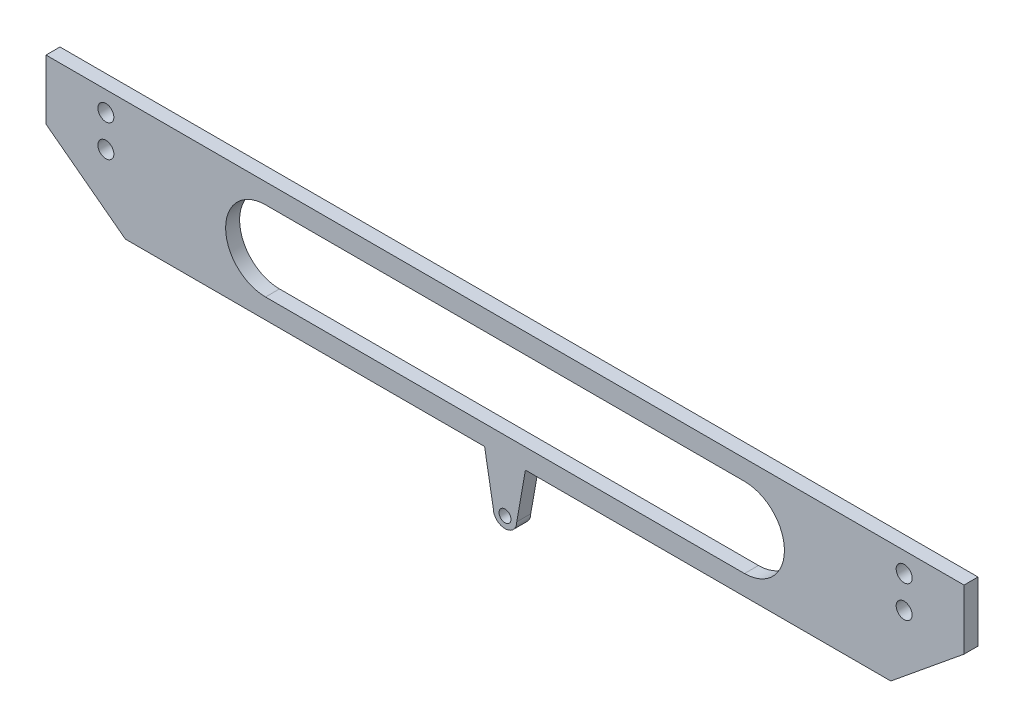
SolidWorks part; units mm, degrees
material "Acrylic (Medium-high impact)"
ref_plane "Front Plane" through (0, 0, 0) normal (0, 0, 1) x (1, 0, 0)
ref_plane "Top Plane" through (0, 0, 0) normal (0, 1, 0) x (1, 0, 0)
ref_plane "Right Plane" through (0, 0, 0) normal (1, 0, 0) x (0, 0, -1)
sketch "Sketch1" plane through (0, 0, 0) normal (0, 0, 1) x (1, 0, 0)
  line L0 (65, 0) -> (-65, 0) construction
  line L1 (-65, 0) -> (0, 65) construction
  line L2 (0, 65) -> (65, 0) construction
  line L3 (0, 65) -> (130, 65) construction
  line L4 (130, 65) -> (195, 0) construction
  circle A0 centre (-65, 0) radius 30
  circle A1 centre (65, 0) radius 30
  circle A2 centre (195, 0) radius 30
  point P4 (0, 0)
  dimension "D2" = 60
  dimension "D1" = 130
  dimension "D3" = 90
  dimension "D4" = 91.9239
  dimension "D5" = 135
  dimension "D6" = 130
sketch "Sketch2" plane through (0, 0, 0) normal (0, 0, 1) x (1, 0, 0)
  line L4 (-56.1612, -8.8388) -> (0, 47.3223)
  line L5 (0, 47.3223) -> (56.1612, -8.8388)
  line L6 (-73.8388, 8.8388) -> (0, 82.6777)
  line L7 (0, 82.6777) -> (73.8388, 8.8388)
  line L19 (56.1612, -8.8388) -> (0, 47.3223)
  circle A0 centre (-65, 0) radius 3.5
  circle A1 centre (65, 0) radius 3.5
  arc A4 (56.1612, -8.8388) -> (73.8388, 8.8388) centre (65, 0) ccw
  arc A5 (-73.8388, 8.8388) -> (-56.1612, -8.8388) centre (-65, 0) ccw
  circle A6 centre (65, 0) radius 3.5
  circle A7 centre (0, 65) radius 1.5
  point P18 (-65, 0)
  dimension "D6" = 3
  dimension "D1" = 25
  dimension "D2" = 90
sketch "Sketch3" plane through (0, 0, 0) normal (0, 0, 1) x (1, 0, 0)
  line L0 (5.5606, 53.0357) -> (0, 47.3223)
  line L1 (-56.1612, -8.8388) -> (0, 47.3223) construction
  line L2 (-73.8388, 8.8388) -> (0, 82.6777) construction
  line L3 (0, 47.3223) -> (-17.6777, 65)
  line L4 (5.5606, 53.0357) -> (124.8223, 52.5)
  line L5 (124.8223, 52.5) -> (186.1612, -8.8388)
  line L6 (-5.1777, 77.5) -> (59.8841, 77.5)
  line L7 (135.1777, 77.5) -> (203.8388, 8.8388)
  line L8 (-17.6777, 65) -> (-5.1777, 77.5)
  line L9 (0, 65) -> (130, 65) construction
  line L10 (0, 47.3223) -> (56.1612, -8.8388) construction
  line L11 (65, 77.5) -> (65, 89.5) construction
  line L12 (59.8841, 77.5) -> (62, 89.5)
  line L13 (70.1159, 77.5) -> (68, 89.5)
  line L14 (70.1159, 77.5) -> (135.1777, 77.5)
  arc A0 (203.8388, 8.8388) -> (186.1612, -8.8388) centre (195, 0) cw
  circle A1 centre (195, 0) radius 3.5
  circle A2 centre (65, 0) radius 3.5 construction
  circle A3 centre (0, 65) radius 1.5
  circle A5 centre (65, 65) radius 1.5
  circle A6 centre (65, 89.5) radius 1.5
  arc A7 (68, 89.5) -> (62, 89.5) centre (65, 88.971) ccw
  dimension "D2" = 3
  dimension "D6" = 3
  dimension "D1" = 25
  dimension "D3" = 12
  dimension "D4" = 80
  dimension "D5" = 3
sketch "Sketch4" plane through (0, 0, 0) normal (0, 0, 1) x (1, 0, 0)
  line L0 (59.8841, 77.5) -> (62.0573, 65.175)
  line L1 (161.6541, 77.5) -> (70.1159, 77.5)
  line L2 (70.1159, 77.5) -> (135.1777, 77.5) construction
  line L3 (65, 65) -> (65, 71.4286) construction
  line L4 (70.1159, 77.5) -> (67.9427, 65.175)
  line L7 (-65, 0) -> (65, 130) construction
  line L8 (65, 130) -> (195, 0) construction
  line L9 (-30.1159, 77.5) -> (59.8841, 77.5)
  line L10 (-30.1159, 77.5) -> (-50, 92.5)
  line L11 (-50, 92.5) -> (-50, 107.5)
  line L12 (-50, 107.5) -> (180, 107.5)
  line L13 (161.6541, 77.5) -> (180, 92.5)
  line L14 (180, 92.5) -> (180, 107.5)
  line L16 (125, 92.5) -> (5, 92.5) construction
  line L17 (125, 82.5) -> (5, 82.5)
  line L18 (125, 102.5) -> (5, 102.5)
  circle A0 centre (65, 65) radius 1.5 construction
  circle A1 centre (65, 65) radius 1.5
  arc A3 (67.9427, 65.175) -> (62.0573, 65.175) centre (65, 65.175) cw
  arc A4 (125, 82.5) -> (125, 102.5) centre (125, 92.5) ccw
  arc A5 (5, 102.5) -> (5, 82.5) centre (5, 92.5) ccw
  point P30 (65, 92.5)
  point P35 (65, 107.5)
  dimension "D8" = 10
  dimension "D2" = 90
  dimension "D1" = 80
  dimension "D3" = 15
  dimension "D4" = 90
  dimension "D5" = 15
  dimension "D6" = 230
  dimension "D9" = 120
extrude "Boss-Extrude1" add sketch "Sketch4" against normal blind 3.5
sketch "Sketch5" plane through (0, 107.5, 0) normal (0, 1, 0) x (1, 0, 0)
  line L0 (65, 3.5) -> (65, 28.3831) construction
  line L1 (-50, 3.5) -> (-20, 3.5)
  line L2 (-50, 3.5) -> (-50, 18.5)
  line L3 (-50, 18.5) -> (-20, 18.5)
  line L4 (-20, 3.5) -> (-20, 18.5)
  line L5 (180, 3.5) -> (-50, 3.5) construction
  line L11 (180, 3.5) -> (150, 3.5)
  line L12 (180, 3.5) -> (180, 18.5)
  line L13 (180, 18.5) -> (150, 18.5)
  line L14 (150, 3.5) -> (150, 18.5)
  circle A3 centre (-35, 11) radius 2
  circle A4 centre (165, 11) radius 2
  dimension "D3" = 200
  dimension "D4" = 4
  dimension "D1" = 30
  dimension "D2" = 15
extrude "Boss-Extrude2" [suppressed] add sketch "Sketch5" against normal blind 3.5
sketch "Sketch6" plane through (0, 0, 0) normal (0, 0, 1) x (1, 0, 0)
  line L1 (180, 107.5) -> (-50, 107.5) construction
  line L2 (65, 107.5) -> (65, 33.717) construction
  circle A0 centre (-35, 102.5) radius 2
  circle A1 centre (-35, 94.5) radius 2
  circle A2 centre (165, 94.5) radius 2
  circle A3 centre (165, 102.5) radius 2
  dimension "D3" = 4
  dimension "D1" = 5
  dimension "D2" = 8
extrude "Cut-Extrude1" cut sketch "Sketch6" against normal blind 10
